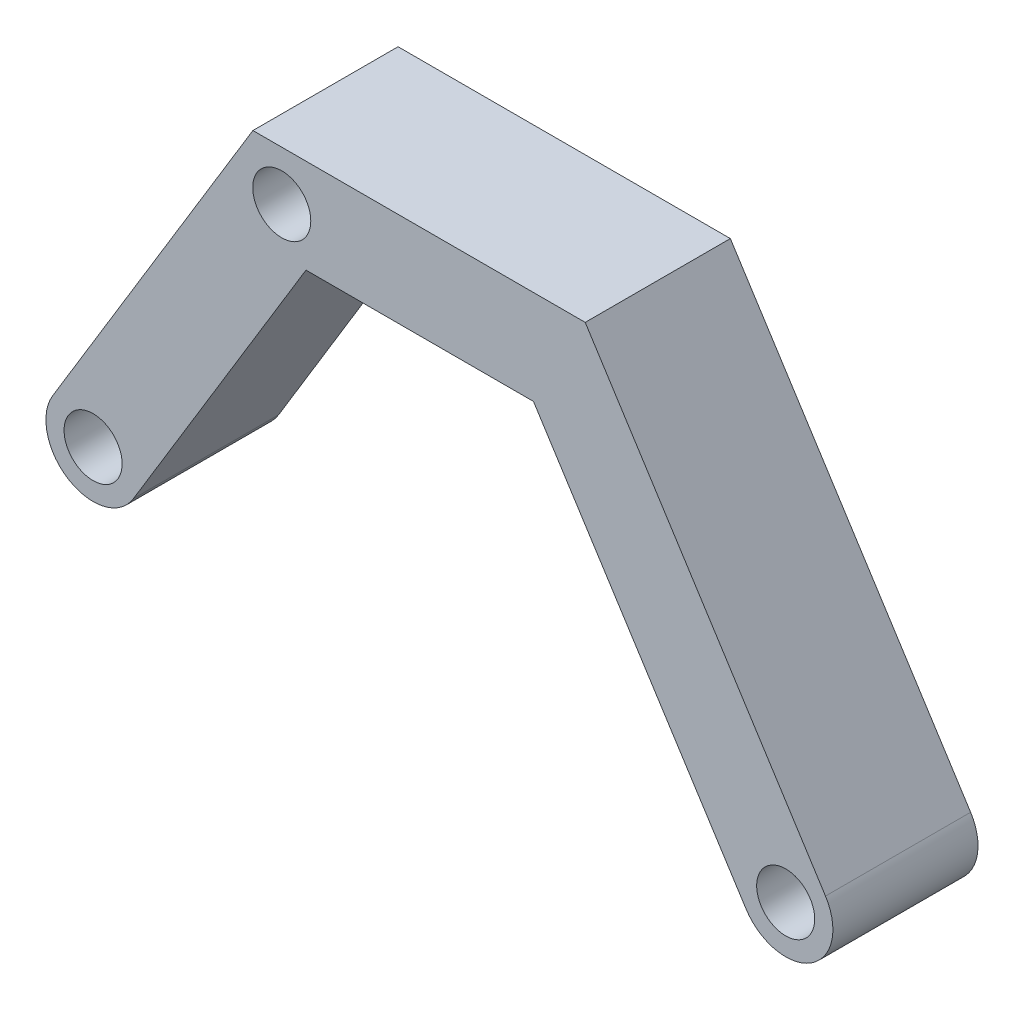
SolidWorks part; units mm, degrees
ref_plane "Płaszczyzna przednia" through (0, 0, 0) normal (0, 0, 1) x (1, 0, 0)
ref_plane "Płaszczyzna górna" through (0, 0, 0) normal (0, 1, 0) x (1, 0, 0)
ref_plane "Płaszczyzna prawa" through (0, 0, 0) normal (1, 0, 0) x (0, 0, -1)
sketch "Szkic1" plane through (0, 0, 0) normal (0, 0, 1) x (1, 0, 0)
  line L6 (3.3395, -8.6165) -> (58.4968, 82.2172)
  line L7 (58.4968, 82.2172) -> (150.0743, 82.2172)
  line L8 (150.0743, 82.2172) -> (216.2944, -21.5966)
  line L9 (25.5631, -22.1114) -> (73.1268, 56.2172)
  line L10 (73.1268, 56.2172) -> (135.8199, 56.2172)
  line L11 (135.8199, 56.2172) -> (194.3742, -35.5789)
  line L12 (150.0743, 82.2172) -> (207.1081, -7.1952) construction
  line L13 (135.8199, 56.2172) -> (185.1879, -21.1775) construction
  circle A0 centre (14.4513, -15.3639) radius 8
  circle A2 centre (205.3343, -28.5877) radius 8
  arc A11 (3.3395, -8.6165) -> (25.5631, -22.1114) centre (14.4513, -15.3639) ccw
  arc A12 (194.3742, -35.5789) -> (216.2944, -21.5966) centre (205.3343, -28.5877) ccw
  point P3 (99.8392, 51.1503)
  point P6 (205.2583, -7.756)
  point P15 (0, 0)
  point P16 (175.5533, -2.6368)
  point P18 (0, 0)
  point P19 (207.0114, -5.6388)
  point P20 (70.4211, 64.9634)
  point P21 (0, -19.6211)
  point P22 (89.6525, 53.357)
  point P23 (-5.1495, -29.3924)
  point P24 (-5.3499, -57.9391)
  point P25 (0, 0)
  point P26 (14.4513, -15.3639)
  point P27 (136.053, 56.2172)
  point P28 (205.3343, -28.5877)
  dimension "D1" = 26
extrude "Dodanie-wyciągnięcie1" add sketch "Szkic1" along normal blind 40
sketch "Szkic2" plane through (0, 0, 40) normal (0, 0, 1) x (1, 0, 0)
  circle A0 centre (66.4465, 68.5834) radius 8
  point P2 (132.8655, 70.413)
  point P4 (66.4465, 68.5834)
extrude "Wytnij-wyciągnięcie2" cut sketch "Szkic2" against normal blind 200 contours A0
